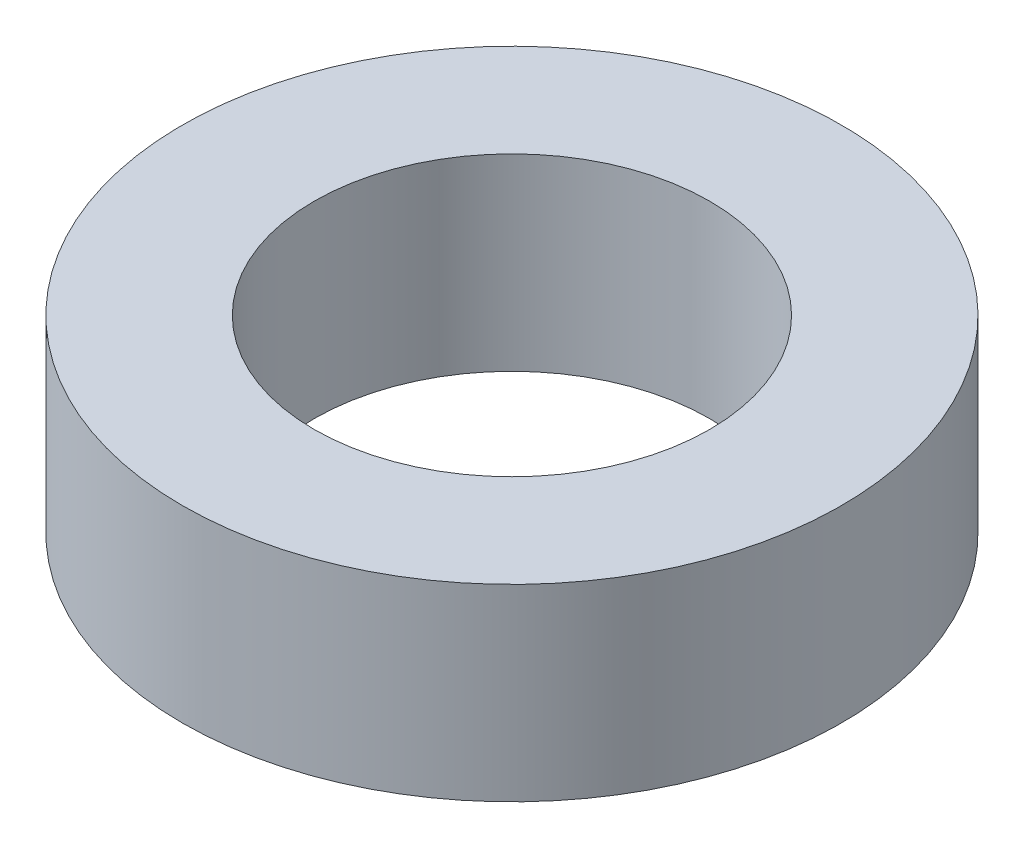
SolidWorks part; units mm, degrees
ref_plane "Alzado" through (0, 0, 0) normal (0, 0, 1) x (1, 0, 0)
ref_plane "Planta" through (0, 0, 0) normal (0, 1, 0) x (1, 0, 0)
ref_plane "Vista lateral" through (0, 0, 0) normal (1, 0, 0) x (0, 0, -1)
sketch "Sketch3" plane through (0, 0, 0) normal (0, 1, 0) x (1, 0, 0)
  circle A0 centre (0, 0) radius 2.1
  circle A1 centre (0, 0) radius 3.5
extrude "Boss-Extrude1" add sketch "Sketch3" along normal blind 2
